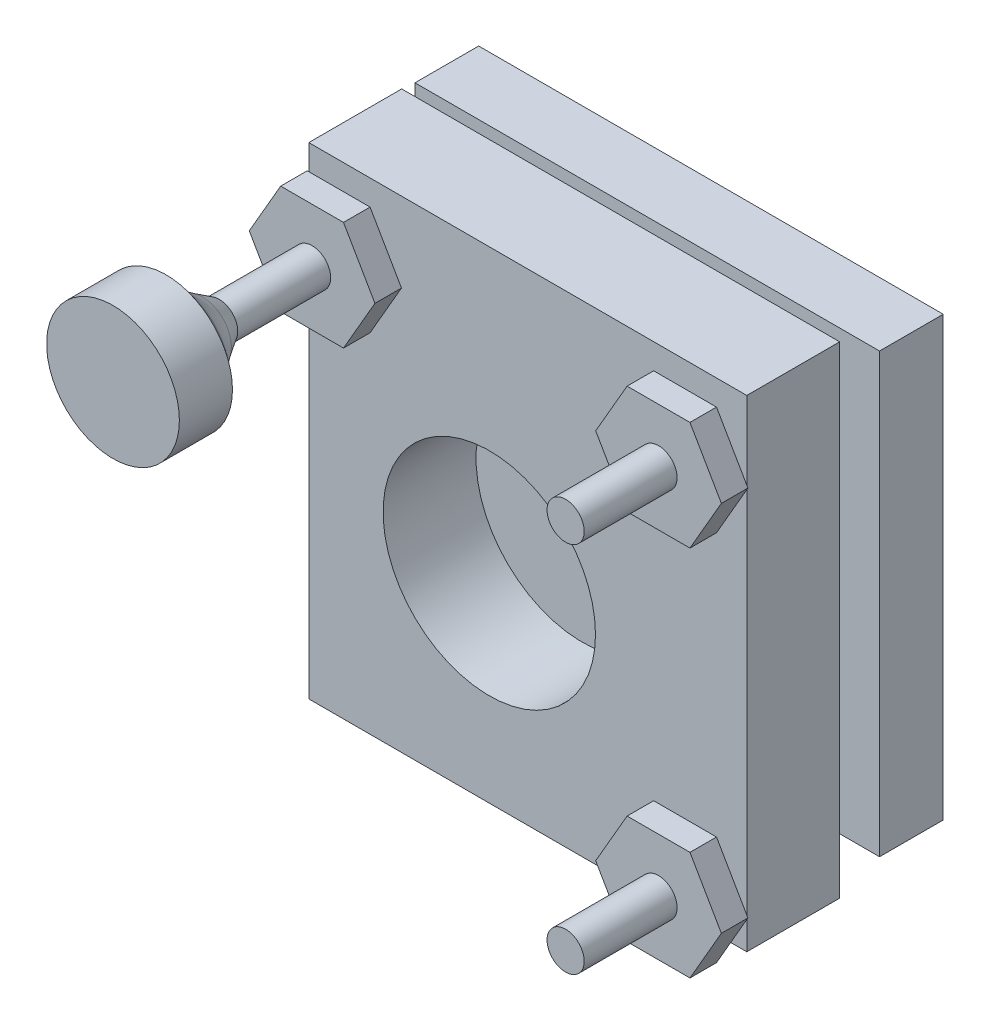
SolidWorks part; units mm, degrees
ref_plane "Alzado" through (0, 0, 0) normal (0, 0, 1) x (1, 0, 0)
ref_plane "Planta" through (0, 0, 0) normal (0, 1, 0) x (1, 0, 0)
ref_plane "Vista lateral" through (0, 0, 0) normal (1, 0, 0) x (0, 0, -1)
sketch "Croquis1" plane through (0, 0, 0) normal (0, 1, 0) x (1, 0, 0)
  line L1 (-16.5, -3.5) -> (16.5, -3.5)
  line L2 (-16.5, -3.5) -> (-16.5, 3.5)
  line L3 (-16.5, 3.5) -> (16.5, 3.5)
  line L4 (16.5, -3.5) -> (16.5, 3.5)
  line L5 (-16.5, -3.5) -> (16.5, 3.5) construction
  line L6 (-16.5, 3.5) -> (16.5, -3.5) construction
  point P0 (0, 0)
  dimension "D1" = 7
  dimension "D2" = 33
extrude "Saliente-Extruir1" add sketch "Croquis1" along normal blind 36.3
sketch "Croquis2" plane through (0, 0, 0) normal (0, -1, 0) x (1, 0, 0)
  line L0 (16.5, 3.5) -> (16.5, -3.5) construction
  line L2 (-6.8, 0) -> (0, 0) construction
  circle A0 centre (-6.8, 0) radius 1.5
  circle A1 centre (9.3, 0) radius 1.5
  dimension "D1" = 3
  dimension "D3" = 16.1
  dimension "D2" = 7.2
extrude "Cortar-Extruir1" cut sketch "Croquis2" against normal blind 5
sketch "Croquis3" plane through (0, 0, 3.5) normal (0, 0, 1) x (1, 0, 0)
  line L0 (16.5, 36.3) -> (16.5, 0) construction
  line L1 (-16.5, 0) -> (16.5, 0) construction
  circle A0 centre (-2.9, 15) radius 8
  dimension "D1" = 16
  dimension "D2" = 19.4
  dimension "D3" = 15
extrude "Cortar-Extruir2" cut sketch "Croquis3" against normal through all
sketch "Croquis4" plane through (0, 0, 3.5) normal (0, 0, 1) x (1, 0, 0)
  line L0 (-16.5, 36.3) -> (16.5, 36.3) construction
  line L1 (-16.5, 36.3) -> (-16.5, 0) construction
  line L2 (16.5, 36.3) -> (16.5, 0) construction
  line L3 (-16.5, 0) -> (16.5, 0) construction
  circle A0 centre (-13.05, 31.5) radius 2.4
  circle A1 centre (13.05, 31.5) radius 2.4
  circle A2 centre (13.05, 3.45) radius 2.4
  dimension "D1" = 4.8
  dimension "D2" = 4.8
  dimension "D3" = 3.45
  dimension "D4" = 3.45
  dimension "D5" = 3.45
extrude "Saliente-Extruir2" add sketch "Croquis4" along normal blind 1.2
sketch "Croquis5" plane through (0, 0, 4.7) normal (0, 0, 1) x (1, 0, 0)
  line L1 (-17.7843, 31.5) -> (-15.4171, 27.4)
  line L2 (-15.4171, 27.4) -> (-10.6829, 27.4)
  line L3 (-10.6829, 27.4) -> (-8.3157, 31.5)
  line L4 (-8.3157, 31.5) -> (-10.6829, 35.6)
  line L5 (-10.6829, 35.6) -> (-15.4171, 35.6)
  line L6 (-15.4171, 35.6) -> (-17.7843, 31.5)
  line L7 (17.7843, 31.5) -> (15.4171, 35.6)
  line L8 (15.4171, 35.6) -> (10.6829, 35.6)
  line L9 (10.6829, 35.6) -> (8.3157, 31.5)
  line L10 (8.3157, 31.5) -> (10.6829, 27.4)
  line L11 (10.6829, 27.4) -> (15.4171, 27.4)
  line L12 (15.4171, 27.4) -> (17.7843, 31.5)
  line L13 (17.7843, 3.45) -> (15.4171, 7.55)
  line L14 (15.4171, 7.55) -> (10.6829, 7.55)
  line L15 (10.6829, 7.55) -> (8.3157, 3.45)
  line L16 (8.3157, 3.45) -> (10.6829, -0.65)
  line L17 (10.6829, -0.65) -> (15.4171, -0.65)
  line L18 (15.4171, -0.65) -> (17.7843, 3.45)
  circle A0 centre (-13.05, 31.5) radius 4.1 construction
  circle A1 centre (13.05, 31.5) radius 4.1 construction
  circle A2 centre (13.05, 3.45) radius 4.1 construction
  dimension "D1" = 8.2
extrude "Saliente-Extruir3" add sketch "Croquis5" along normal blind 2
sketch "Croquis6" plane through (0, 0, 6.7) normal (0, 0, 1) x (1, 0, 0)
  line L0 (-15.4171, 35.6) -> (-10.6829, 27.4) construction
  line L1 (10.6829, 35.6) -> (15.4171, 27.4) construction
  line L3 (10.6829, 7.55) -> (15.4171, -0.65) construction
  circle A0 centre (-13.05, 31.5) radius 1.4
  circle A1 centre (13.05, 31.5) radius 1.4
  circle A2 centre (13.05, 3.45) radius 1.4
  dimension "D1" = 2.8
extrude "Saliente-Extruir4" add sketch "Croquis6" along normal blind 7
sketch "Croquis7" plane through (0, 0, 6.7) normal (0, 0, 1) x (1, 0, 0)
  line L0 (-17.7843, 31.5) -> (-8.3157, 31.5)
ref_plane "Plano1" through (0, 31.5, 0) normal (0, -1, 0) x (1, 0, 0)
sketch "Croquis8" plane through (0, 31.5, 0) normal (0, -1, 0) x (1, 0, 0)
  line L0 (-14.45, 13.7) -> (-15.2324, 14.963)
  line L1 (-16.9089, 16.8202) -> (-18.05, 17.7)
  line L2 (-18.05, 17.7) -> (-18.05, 21.7)
  line L3 (-18.05, 21.7) -> (-13.05, 21.7)
  line L4 (-13.05, 21.7) -> (-13.05, 13.7) construction
  line L5 (-11.65, 13.7) -> (-14.45, 13.7) construction
  line L6 (-14.45, 13.7) -> (-13.05, 13.7)
  line L7 (-13.05, 21.7) -> (-13.05, 13.7)
  arc A0 (-15.2324, 14.963) -> (-16.9089, 16.8202) centre (-21.1831, 11.2766) ccw
  dimension "D3" = 7
  dimension "D1" = 4
  dimension "D2" = 4
  dimension "D4" = 5
revolve "Revolución1" add sketch "Croquis8" angle 360 about L4
ref_plane "Plano2" through (0, 0, -5.5) normal (0, 0, -1) x (-1, 0, 0)
sketch "Croquis9" plane through (0, 0, -5.5) normal (0, 0, -1) x (-1, 0, 0)
  line L1 (-17.5, 35.2) -> (17.5, 35.2)
  line L2 (-17.5, 35.2) -> (-17.5, 2.2)
  line L3 (-17.5, 2.2) -> (17.5, 2.2)
  line L4 (17.5, 35.2) -> (17.5, 2.2)
  line L6 (-16.5, 36.3) -> (-16.5, 0) construction
  line L8 (-16.5, 36.3) -> (16.5, 36.3) construction
  dimension "D1" = 35
  dimension "D2" = 33
  dimension "D3" = 1
  dimension "D4" = 1.1
extrude "Saliente-Extruir5" add sketch "Croquis9" along normal blind 4.8 separate body
sketch "Croquis10" plane through (0, 0, -10.3) normal (0, 0, -1) x (-1, 0, 0)
  circle A0 centre (2.9, 15) radius 5.8397
  circle A1 centre (2.9, 15) radius 8 construction
  dimension "D1" = 11.6793
extrude "Saliente-Extruir6" add sketch "Croquis10" along normal blind 1
sketch "Croquis11" plane through (0, 0, -11.3) normal (0, 0, -1) x (-1, 0, 0)
  circle A0 centre (2.9, 15) radius 14
  dimension "D1" = 28
extrude "Saliente-Extruir7" add sketch "Croquis11" along normal blind 5
sketch "Croquis12" plane through (0, 0, -16.3) normal (0, 0, -1) x (-1, 0, 0)
  circle A0 centre (2.9, 15) radius 8
  circle A1 centre (2.9, 15) radius 14 construction
  dimension "D1" = 16
extrude "Cortar-Extruir3" cut sketch "Croquis12" against normal blind 1
ref_point "Punto1"
ref_plane "Plano3" through (0, 15, 0) normal (0, 1, 0) x (1, 0, 0)
sketch "Croquis13" plane through (0, 15, 0) normal (0, 1, 0) x (1, 0, 0)
  line L0 (-2.9, 15.3) -> (-365.0579, 377.4579)
  line L1 (-2.9, 15.3) -> (151.5841, 169.7841)
  line L2 (-2.9, 15.3) -> (-2.9, 50.4322) construction
  dimension "D1" = 90
  dimension "D2" = 45
sketch "Croquis14" plane through (0, 0, -15.3) normal (0, 0, -1) x (-1, 0, 0)
  line L0 (-5.1, 15) -> (10.9, 15) construction
  line L1 (2.9, 15) -> (-151.5841, 15) construction
  line L2 (2.9, 15) -> (365.0579, 15) construction
  line L4 (2.9, 23) -> (2.9, 7) construction
  circle A0 centre (2.9, 15) radius 8 construction
  circle A1 centre (2.9, 15) radius 8 construction
